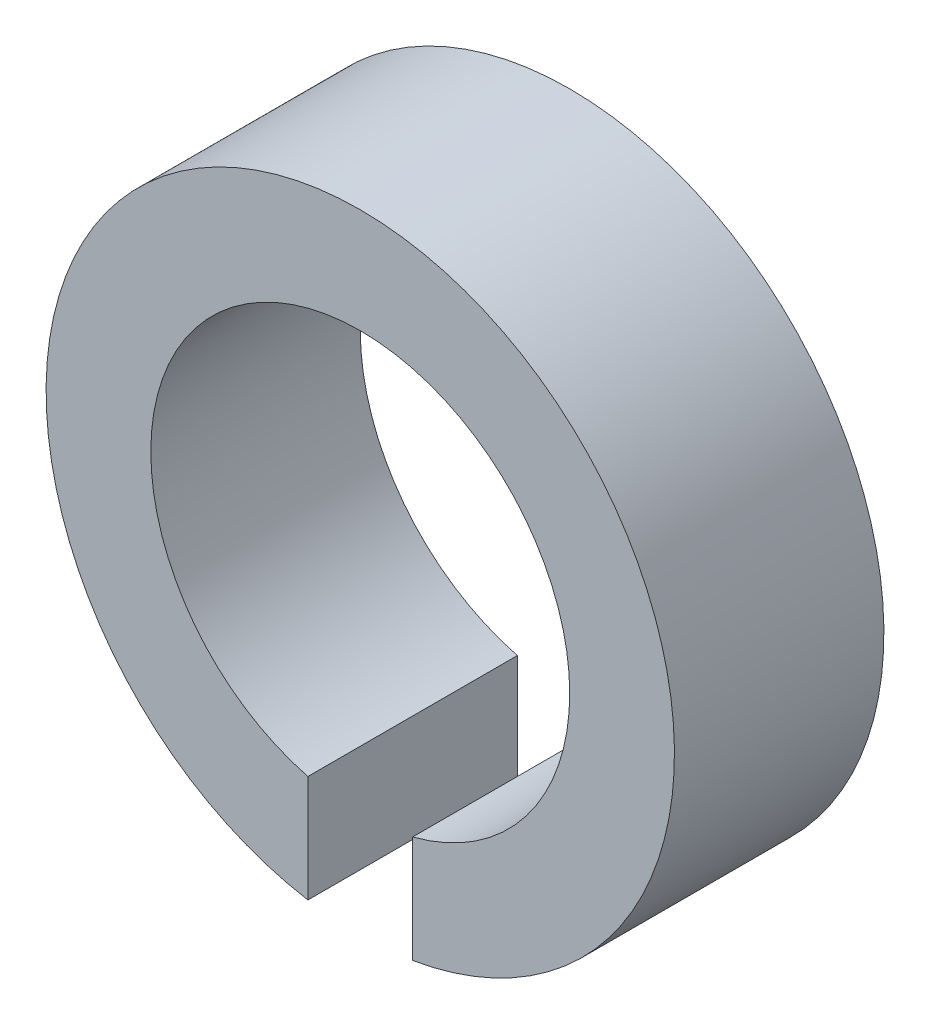
SolidWorks part; units mm, degrees
ref_plane "Plane1" through (0, 0, 0) normal (0, 0, 1) x (1, 0, 0)
ref_plane "Plane2" through (0, 0, 0) normal (0, 1, 0) x (1, 0, 0)
ref_plane "Plane3" through (0, 0, 0) normal (1, 0, 0) x (0, 0, -1)
sketch "Esquisse1" plane through (0, 0, 0) normal (0, 0, 1) x (1, 0, 0)
  line L0 (0, 0) -> (0, -14) construction
  line L1 (1.5, -5.8095) -> (1.5, -8.8741)
  line L2 (-1.5, -5.8095) -> (-1.5, -8.8741)
  arc A0 (1.5, -8.8741) -> (-1.5, -8.8741) centre (0, 0) ccw
  arc A1 (1.5, -5.8095) -> (-1.5, -5.8095) centre (0, 0) ccw
  dimension "D1" = 12
  dimension "D3" = 18
  dimension "D2" = 3
extrude "Base-Extrusion" add sketch "Esquisse1" along normal blind 6
